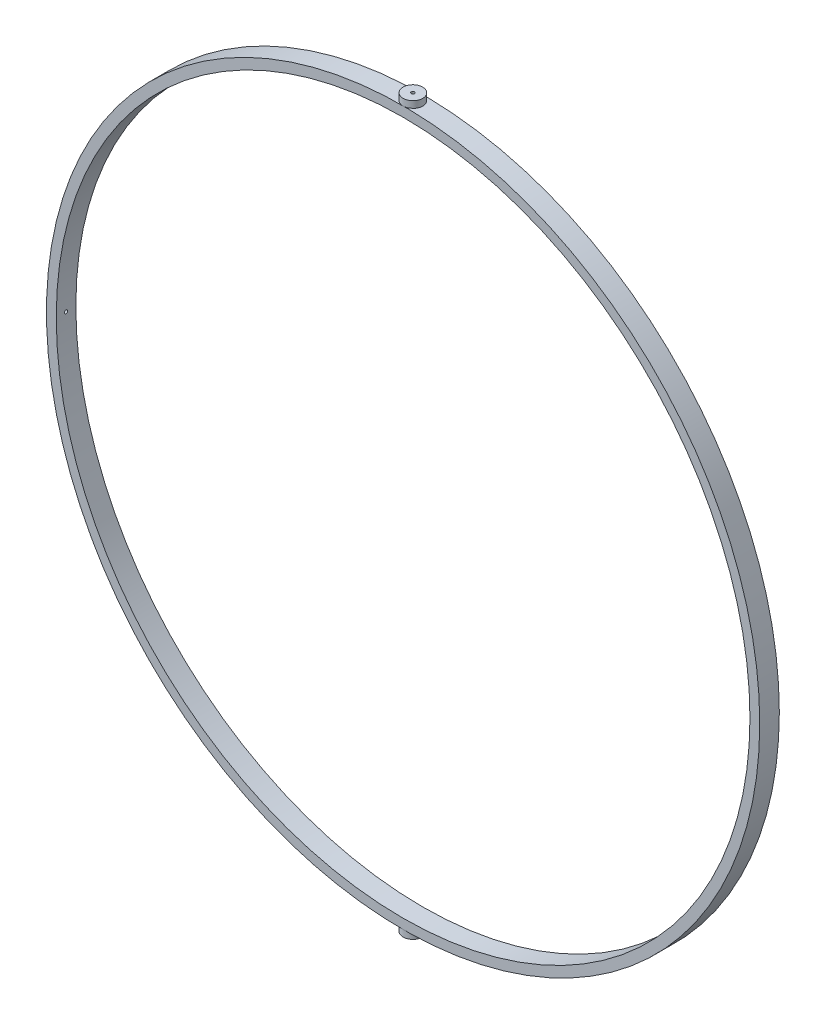
SolidWorks part; units mm, degrees
ref_plane "Front Plane" through (0, 0, 0) normal (0, 0, 1) x (1, 0, 0)
ref_plane "Top Plane" through (0, 0, 0) normal (0, 1, 0) x (1, 0, 0)
ref_plane "Right Plane" through (0, 0, 0) normal (1, 0, 0) x (0, 0, -1)
sketch "Sketch1" plane through (0, 0, 0) normal (0, 0, 1) x (1, 0, 0)
  line L1 (106.2472, -106.2472) -> (-106.2472, -106.2472) construction
  line L2 (106.2472, -106.2472) -> (106.2472, 106.2472) construction
  line L3 (106.2472, 106.2472) -> (-106.2472, 106.2472) construction
  line L4 (-106.2472, -106.2472) -> (-106.2472, 106.2472) construction
  line L5 (106.2472, -106.2472) -> (-106.2472, 106.2472) construction
  line L6 (106.2472, 106.2472) -> (-106.2472, -106.2472) construction
  circle A0 centre (0, 0) radius 109.2472
  circle A1 centre (0, 0) radius 106.2472
extrude "Boss-Extrude1" add sketch "Sketch1" along normal blind 6
ref_plane "Plane1" through (0, -106.2472, 0) normal (0, 1, 0) x (1, 0, 0)
sketch "Sketch3" plane through (0, -106.2472, 0) normal (0, 1, 0) x (1, 0, 0)
  line L0 (0, 2.3142) -> (0, -8.3142) construction
  line L1 (79.6414, -3) -> (-84.362, -3) construction
  line L2 (106.2472, 0) -> (-106.2472, 0) construction
  circle A0 centre (0, -3) radius 3
  circle A1 centre (0, -3) radius 0.5
  point P7 (0, -3)
  dimension "D1" = 3
extrude "Boss-Extrude2" add sketch "Sketch3" against normal blind 5 separate body
ref_plane "Plane2" through (0, 106.2472, 0) normal (0, 1, 0) x (1, 0, 0)
sketch "Sketch4" plane through (0, 106.2472, 0) normal (0, 1, 0) x (1, 0, 0)
  circle A0 centre (0, -3) radius 3
  circle A1 centre (0, -3) radius 0.5
extrude "Boss-Extrude3" add sketch "Sketch4" along normal blind 5 separate body
ref_plane "Plane3" through (106.2472, 0, 0) normal (-1, 0, 0) x (0, 0, 1)
ref_plane "Plane5" through (108.2472, 0, 0) normal (-1, 0, 0) x (0, 0, 1)
sketch "Sketch8" plane through (108.2472, 0, 0) normal (-1, 0, 0) x (0, 0, 1)
  line L0 (55, 0) -> (-55, 0) construction
  line L1 (6, -109.2472) -> (6, 109.2472) construction
  circle A0 centre (3, 0) radius 0.5
  dimension "D1" = 3
extrude "Cut-Extrude7" cut sketch "Sketch8" along normal blind 3
ref_plane "Plane6" through (-106.2472, 0, 0) normal (-1, 0, 0) x (0, 0, 1)
ref_plane "Plane7" through (-108.2472, 0, 0) normal (-1, 0, 0) x (0, 0, 1)
sketch "Sketch9" plane through (-108.2472, 0, 0) normal (-1, 0, 0) x (0, 0, 1)
  line L0 (55, 0) -> (-55, 0) construction
  line L1 (0, 106.2472) -> (0, -106.2472) construction
  circle A0 centre (3, 0) radius 0.5
  dimension "D1" = 3
extrude "Cut-Extrude8" cut sketch "Sketch9" against normal blind 3
